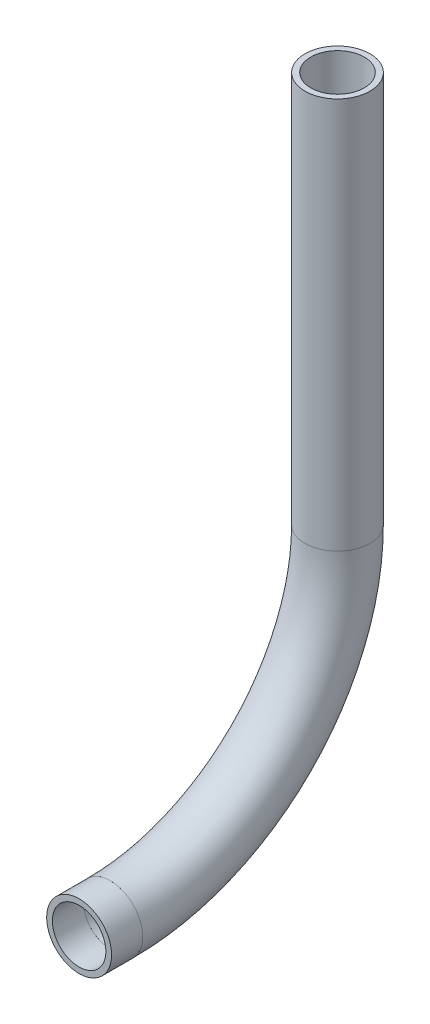
SolidWorks part; units mm, degrees
ref_plane "Front Plane" through (0, 0, 0) normal (0, 0, 1) x (1, 0, 0)
ref_plane "Top Plane" through (0, 0, 0) normal (0, 1, 0) x (1, 0, 0)
ref_plane "Right Plane" through (0, 0, 0) normal (1, 0, 0) x (0, 0, -1)
sketch "Sketch1" plane through (0, 0, 0) normal (1, 0, 0) x (0, 0, -1)
  line L0 (-303.1446, 600.0345) -> (-300.0923, 600.0345)
  line L1 (-277.8673, 622.2595) -> (-277.8673, 660.5723)
  line L2 (-303.1446, 596.8595) -> (-303.1446, 603.2095) construction
  arc A0 (-300.0923, 600.0345) -> (-277.8673, 622.2595) centre (-300.0923, 622.2595) ccw
  dimension "D1" = 22.225
other "Pipe 0.5 SCH 40(1)"
ref_plane "Plane1" through (0, 600.0345, 303.1446) normal (0, 0, -1) x (0, 1, 0)
sketch "Sketch11" plane through (0, 600.0345, 303.1446) normal (0, 0, -1) x (0, 1, 0)
  circle A0 centre (0, 0) radius 3.175
  circle A1 centre (0, 0) radius 2.6162
  point P5 (0, 0)
  dimension "In_dia" = 6.35
  dimension "Out_dia" = 5.2324
